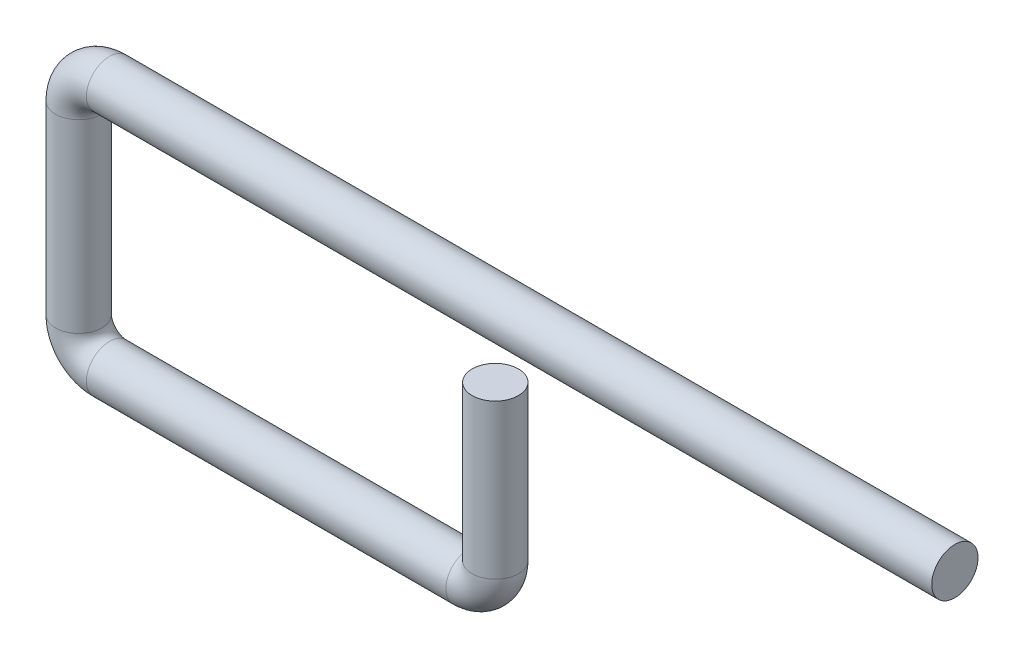
SolidWorks part; units mm, degrees
ref_plane "Ön Düzlem" through (0, 0, 0) normal (0, 0, 1) x (1, 0, 0)
ref_plane "Üst Düzlem" through (0, 0, 0) normal (0, 1, 0) x (1, 0, 0)
ref_plane "Sağ Düzlem" through (0, 0, 0) normal (1, 0, 0) x (0, 0, -1)
sketch "Sketch1" plane through (0, 0, 0) normal (0, 0, 1) x (1, 0, 0)
  line L0 (0, 0) -> (-137, 0)
  line L1 (-142, -5) -> (-142, -35)
  line L2 (-137, -40) -> (-78.75, -40)
  line L3 (-74.482, -35.732) -> (-74.482, -10.732)
  arc A0 (-137, 0) -> (-142, -5) centre (-137, -5) ccw
  arc A1 (-142, -35) -> (-137, -40) centre (-137, -35) ccw
  arc A2 (-78.75, -40) -> (-74.482, -35.732) centre (-78.75, -35.732) ccw
  dimension "D1" = 5
  dimension "D2" = 5
  dimension "D3" = 137
  dimension "D4" = 30
  dimension "D5" = 58.25
  dimension "D6" = 25
sketch "Sketch2" plane through (0, 0, 0) normal (1, 0, 0) x (0, 0, -1)
  circle A0 centre (0, 0) radius 3.75
  dimension "D1" = 7.5
sweep "Sweep1" add profiles "Sketch2" path "Sketch1"
